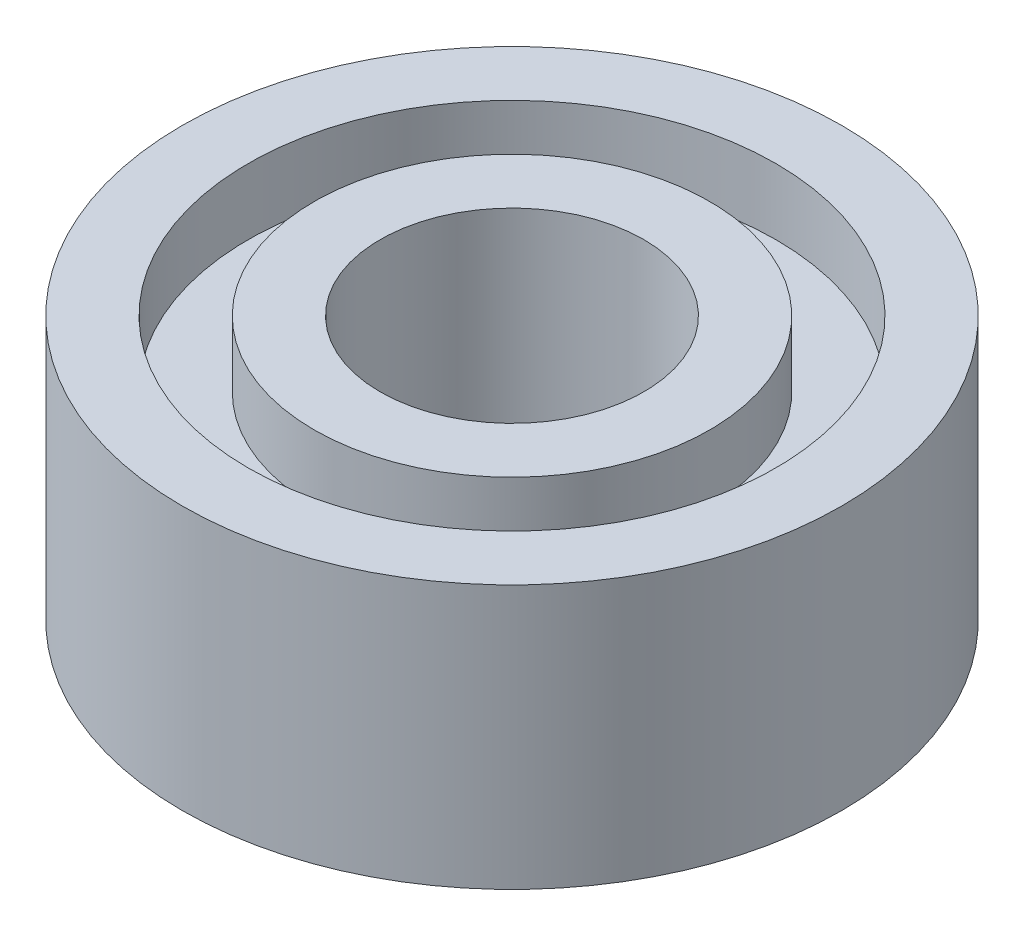
SolidWorks part; units mm, degrees
ref_plane "Front Plane" through (0, 0, 0) normal (0, 0, 1) x (1, 0, 0)
ref_plane "Top Plane" through (0, 0, 0) normal (0, 1, 0) x (1, 0, 0)
ref_plane "Right Plane" through (0, 0, 0) normal (1, 0, 0) x (0, 0, -1)
sketch "Sketch1" plane through (0, 0, 0) normal (0, 1, 0) x (1, 0, 0)
  circle A0 centre (0, 0) radius 2
  circle A1 centre (0, 0) radius 5
  dimension "D1" = 10
  dimension "D2" = 4
extrude "Boss-Extrude1" add sketch "Sketch1" along normal blind 4
sketch "Sketch2" plane through (0, 4, 0) normal (0, 1, 0) x (1, 0, 0)
  circle A2 centre (0, 0) radius 4
  circle A3 centre (0, 0) radius 4
  circle A5 centre (0, 0) radius 3
  circle A6 centre (0, 0) radius 3
  dimension "D1" = 1
  dimension "D2" = 1
extrude "Cut-Extrude1" cut sketch "Sketch2" against normal blind 1
sketch "Sketch3" plane through (0, 0, 0) normal (0, -1, 0) x (1, 0, 0)
  circle A2 centre (0, 0) radius 3
  circle A3 centre (0, 0) radius 3
  circle A5 centre (0, 0) radius 4
  circle A6 centre (0, 0) radius 4
  dimension "D1" = 2
  dimension "D2" = 2
extrude "Cut-Extrude2" cut sketch "Sketch3" against normal blind 1
